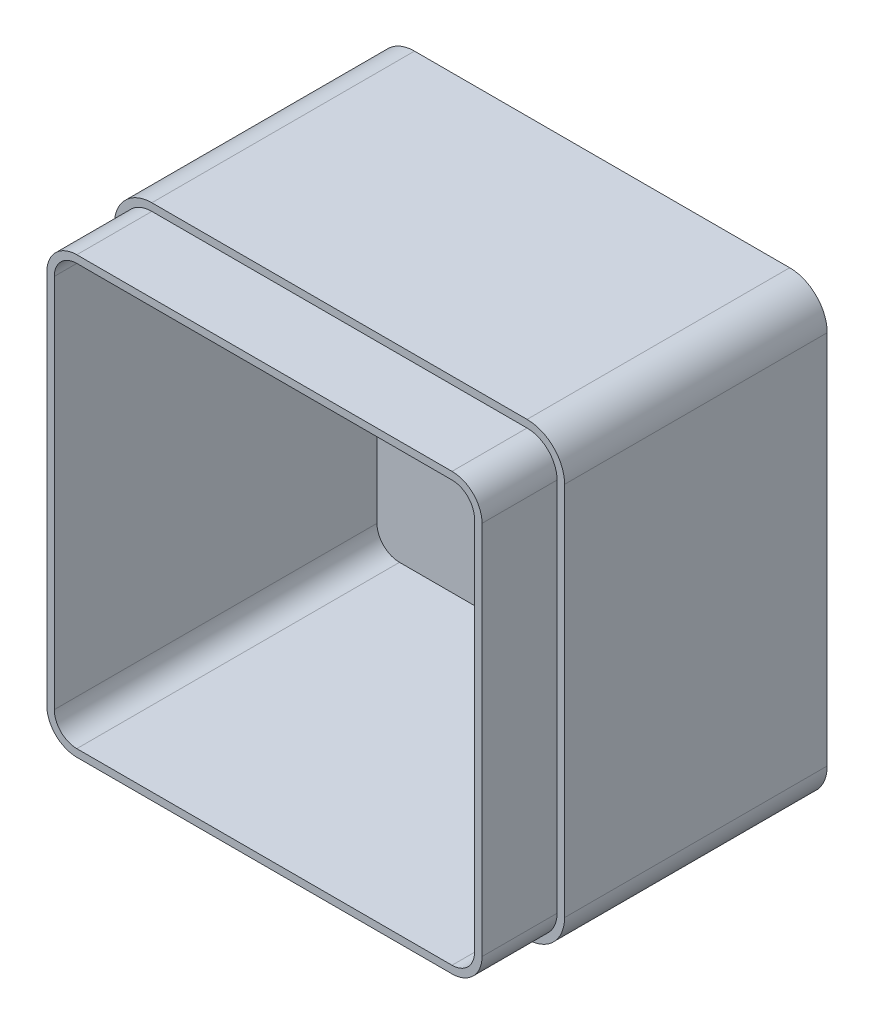
SolidWorks part; units mm, degrees
ref_plane "Front Plane" through (0, 0, 0) normal (0, 0, 1) x (1, 0, 0)
ref_plane "Top Plane" through (0, 0, 0) normal (0, 1, 0) x (1, 0, 0)
ref_plane "Right Plane" through (0, 0, 0) normal (1, 0, 0) x (0, 0, -1)
sketch "Sketch1" plane through (0, 0, 0) normal (0, 0, 1) x (1, 0, 0)
  line L1 (-29.7698, 36.9821) -> (90.2302, 36.9821)
  line L2 (-29.7698, 36.9821) -> (-29.7698, -83.0179)
  line L3 (-29.7698, -83.0179) -> (90.2302, -83.0179)
  line L4 (90.2302, 36.9821) -> (90.2302, -83.0179)
  dimension "D1" = 120
  dimension "D2" = 120
extrude "Boss-Extrude1" add sketch "Sketch1" along normal blind 90
fillet "Fillet1" radius 10 4 edges at (-29.7698, -83.0179, 45) (90.2302, -83.0179, 45) (-29.7698, 36.9821, 45) (90.2302, 36.9821, 45)
shell "Shell1" thickness 4
sketch "Sketch2" plane through (0, 0, 90) normal (0, 0, 1) x (1, 0, 0)
  line L0 (-27.7698, 26.9821) -> (-27.7698, -73.0179)
  line L1 (-19.7698, -81.0179) -> (80.2302, -81.0179)
  line L2 (88.2302, -73.0179) -> (88.2302, 26.9821)
  line L3 (80.2302, 34.9821) -> (-19.7698, 34.9821)
  line L4 (-29.7698, 26.9821) -> (-29.7698, -73.0179)
  line L5 (-19.7698, -83.0179) -> (80.2302, -83.0179)
  line L6 (90.2302, -73.0179) -> (90.2302, 26.9821)
  line L7 (80.2302, 36.9821) -> (-19.7698, 36.9821)
  line L8 (-29.7698, 26.9821) -> (-29.7698, -73.0179)
  line L9 (-19.7698, -83.0179) -> (80.2302, -83.0179)
  line L10 (90.2302, -73.0179) -> (90.2302, 26.9821)
  line L11 (80.2302, 36.9821) -> (-19.7698, 36.9821)
  arc A0 (-27.7698, -73.0179) -> (-19.7698, -81.0179) centre (-19.7698, -73.0179) ccw
  arc A1 (80.2302, -81.0179) -> (88.2302, -73.0179) centre (80.2302, -73.0179) ccw
  arc A2 (88.2302, 26.9821) -> (80.2302, 34.9821) centre (80.2302, 26.9821) ccw
  arc A3 (-19.7698, 34.9821) -> (-27.7698, 26.9821) centre (-19.7698, 26.9821) ccw
  arc A4 (-29.7698, -73.0179) -> (-19.7698, -83.0179) centre (-19.7698, -73.0179) ccw
  arc A5 (80.2302, -83.0179) -> (90.2302, -73.0179) centre (80.2302, -73.0179) ccw
  arc A6 (90.2302, 26.9821) -> (80.2302, 36.9821) centre (80.2302, 26.9821) ccw
  arc A7 (-19.7698, 36.9821) -> (-29.7698, 26.9821) centre (-19.7698, 26.9821) ccw
  arc A8 (-29.7698, -73.0179) -> (-19.7698, -83.0179) centre (-19.7698, -73.0179) ccw
  arc A9 (80.2302, -83.0179) -> (90.2302, -73.0179) centre (80.2302, -73.0179) ccw
  arc A10 (90.2302, 26.9821) -> (80.2302, 36.9821) centre (80.2302, 26.9821) ccw
  arc A11 (-19.7698, 36.9821) -> (-29.7698, 26.9821) centre (-19.7698, 26.9821) ccw
  dimension "D1" = 0
  dimension "D2" = 2
extrude "Cut-Extrude2" cut sketch "Sketch2" against normal blind 20 flip side to cut contours L0 A0 L1 A1 L2 A2 L3 A3
